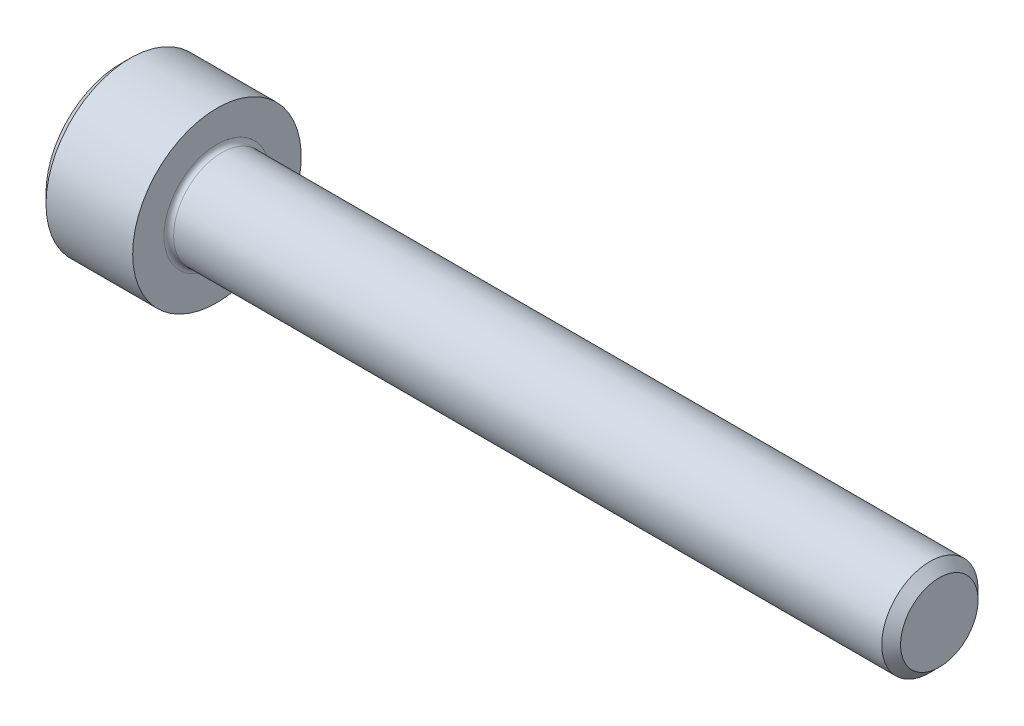
SolidWorks part; units mm, degrees
revolve "Base-Revolve" add sketch "BodySke"
sketch "BodySke" plane through (0, 0, 0) normal (0, 0, 1) x (1, 0, 0)
  line L0 (0, 0) -> (0, 3.1)
  line L1 (0.4, 3.5) -> (4, 3.5)
  line L2 (4, 3.5) -> (4, 2)
  line L3 (4, 2) -> (33.61, 2)
  line L4 (34, 1.61) -> (34, 0)
  line L5 (34, 0) -> (0, 0)
  line L6 (-31.75, 0) -> (127, 0) construction
  line L7 (0, 3.1) -> (0.4, 3.5)
  line L8 (34, 1.61) -> (33.61, 2)
  line L9 (0, -3.1) -> (0.4, -3.5) construction
  line L10 (34, -1.61) -> (33.61, -2) construction
  line L11 (4.7, 9.525) -> (4.7, 3.175) construction
  line L12 (14, 9.525) -> (14, 3.175) construction
  line L13 (-16, 9.525) -> (-16, 3.175) construction
  dimension "Diameter" = 4
  dimension "Head_ht" = 4
  dimension "Length" = 30
  dimension "Body_ch_ang" = 45
  dimension "Head_dia" = 7
  dimension "Head_ch_ang" = 45
  dimension "Minor_dia" = 3.22
  dimension "Advance" = 0.7
  dimension "Thread_nom" = 20
  dimension "Thread_length" = 50
  dimension "Head_ch_ht" = 0.4
cosmetic thread "ThreadCosmetic" [suppressed]
fillet "Fillet1" radius 0.2 1 edges at (4, 0, 2)
ref_plane "Plane1" through (0, 0, 0) normal (0, 0, 1) x (1, 0, 0)
ref_plane "Plane2" through (0, 0, 0) normal (0, 1, 0) x (1, 0, 0)
ref_plane "Plane3" through (0, 0, 0) normal (1, 0, 0) x (0, 0, -1)
sketch "Sketch2" plane through (0, 0, 0) normal (0, 0, 1) x (1, 0, 0)
  line L0 (0, 1.5355) -> (2, 1.5355)
  line L1 (2, 1.5355) -> (2.8865, 0)
  line L2 (-31.75, 0) -> (127, 0) construction
  line L3 (2.8865, 0) -> (0, 0)
  line L4 (0, 0) -> (0, 1.5355)
  line L5 (0, 3.1) -> (0, -3.1) construction
  line L6 (0, 0) -> (47.625, 0) construction
  line L7 (4, -3.5) -> (4, 3.5) construction
  dimension "D1" = 1.5355
  dimension "D2" = 60
revolve "Hex-PreBroach" cut sketch "Sketch2" angle 360 about L6
sketch "Sketch3" plane through (0, 0, 0) normal (-1, 0, 0) x (0, 0.5, 0.866)
  line L0 (0.8865, 1.5355) -> (-0.8865, 1.5355)
  line L1 (-0.8865, 1.5355) -> (-1.773, 0)
  line L2 (0.8865, 1.5355) -> (1.773, 0)
  line L3 (0.8865, -1.5355) -> (1.773, 0)
  line L4 (0.8865, -1.5355) -> (-0.8865, -1.5355)
  line L5 (-0.8865, -1.5355) -> (-1.773, 0)
  dimension "D1" = 1.5355
  dimension "D2" = 1.5355
  dimension "Hex_size" = 3.071
extrude "Hex" cut sketch "Sketch3" against normal blind 2
sketch "Sketch4" plane through (0, 0, 0) normal (-1, 0, 0) x (0, 0, 1)
  line L0 (0, 0) -> (1.7399, 0)
  line L1 (0, 0) -> (6.1484, 3.5498) construction
  line L2 (0, 0) -> (0.8699, 1.5068)
  line L3 (1.4457, 0.3947) -> (1.6607, 0.5189)
  line L4 (1.0647, 1.0546) -> (1.2797, 1.1788)
  arc A0 (1.4457, 0.3947) -> (1.0647, 1.0546) centre (0, 0) ccw
  arc A1 (1.7399, 0) -> (1.6607, 0.5189) centre (0, 0) ccw
  arc A2 (0.8699, 1.5068) -> (1.2797, 1.1788) centre (0, 0) cw
  dimension "D1" = 30
  dimension "D2" = 60
  dimension "Spline_p_dim" = 0.762
  dimension "D3" = 0.381
extrude "Spline" [suppressed] cut sketch "Sketch4" against normal blind 2
pattern_circular "CirPattern1" [suppressed] count 6 every 60
sketch "Sketch5" plane through (0, 0, 0) normal (0, 0, 1) x (1, 0, 0)
  line L0 (-31.75, 0) -> (127, 0) construction
  line L2 (0, 3.1) -> (0, -3.1) construction
  circle A0 centre (1.6, 0) radius 0.675
  dimension "Drilled_hole_dia" = 1.35
  dimension "Drilled_hole_loc" = 1.6
extrude "Hole" [suppressed] cut sketch "Sketch5" against normal through all and the other way through all
pattern_circular "Drilled-4" [suppressed] count 2 every 60
pattern_circular "Drilled-6" [suppressed] count 3 every 60
sketch "ThdSchSke" plane through (0, 0, 0) normal (0, 0, 1) x (1, 0, 0)
  line L0 (14, -1.61) -> (13.7269, -2)
  line L1 (14, -1.61) -> (14.2731, -2)
  line L2 (14.2731, -2) -> (14.2731, -2.5)
  line L3 (-3.175, 0) -> (5.1513, 0) construction
  line L5 (14.2731, -2.5) -> (13.7269, -2.5)
  line L6 (13.7269, -2.5) -> (13.7269, -2)
  line L7 (0, 3.1) -> (0, -3.1) construction
  dimension "Thread_minor" = 3.22
  dimension "Diameter" = 4
  dimension "Start" = 14
revolve "ThreadSchematic" [suppressed] cut sketch "ThdSchSke" angle 360 about L3
pattern_linear "ThdSchPat" [suppressed]
equation "\"D2@Sketch3\" = \"Hex_size@Sketch3\" / 2"
equation "\"D1@Sketch3\" = \"Hex_size@Sketch3\" / 2"
equation "\"D1@Sketch2\" = \"Hex_size@Sketch3\" / 2"
equation "\"D3@Sketch4\" = \"Spline_p_dim@Sketch4\" / 2"
equation "\"Thread_minor@ThreadCosmetic\"  =  \"Minor_dia@BodySke\""
equation "\"D2@CirPattern1\" = 360 / \"Num_teeth@CirPattern1\""
equation "\"Wall_thickness@Sketch2\" = \"Head_ht@BodySke\" - \"Key_eng@Hex\""
equation "\"Thread_length@ThreadCosmetic\" = ((sgn( (\"Length@BodySke\" - \"Advance@BodySke\" ) - \"Thread_nom@BodySke\" )-1)*( (\"Length@BodySke\" - \"Advance@BodySke\" ) - \"Thread_nom@BodySke\" ))/-2+ \"Thread_nom@BodySke\""
equation "\"Thread_minor@ThdSchSke\" = \"Minor_dia@BodySke\""
equation "\"Diameter@ThdSchSke\" = \"Diameter@BodySke\""
equation "\"Overcut@ThdSchSke\" = \"Diameter@BodySke\" * 1.25"
equation "\"Start@ThdSchSke\" = \"Head_ht@BodySke\" + \"Length@BodySke\" - \"Thread_length@ThreadCosmetic\"  '---Non-countersunk---"
equation "\"Num_threads@ThdSchPat\" = int( \"Thread_length@ThreadCosmetic\" / \"Advance@BodySke\" + 0.999 )  + 1"
equation "\"Advance@ThdSchPat\" = \"Thread_length@ThreadCosmetic\" /  (\"Num_threads@ThdSchPat\" - 1) 'relax it"
equation "\"Num_threads@ThdSchPat\" = \"Num_threads@ThdSchPat\" - sgn( \"Num_threads@ThdSchPat\" - 1) '---chamfered tips only---"
